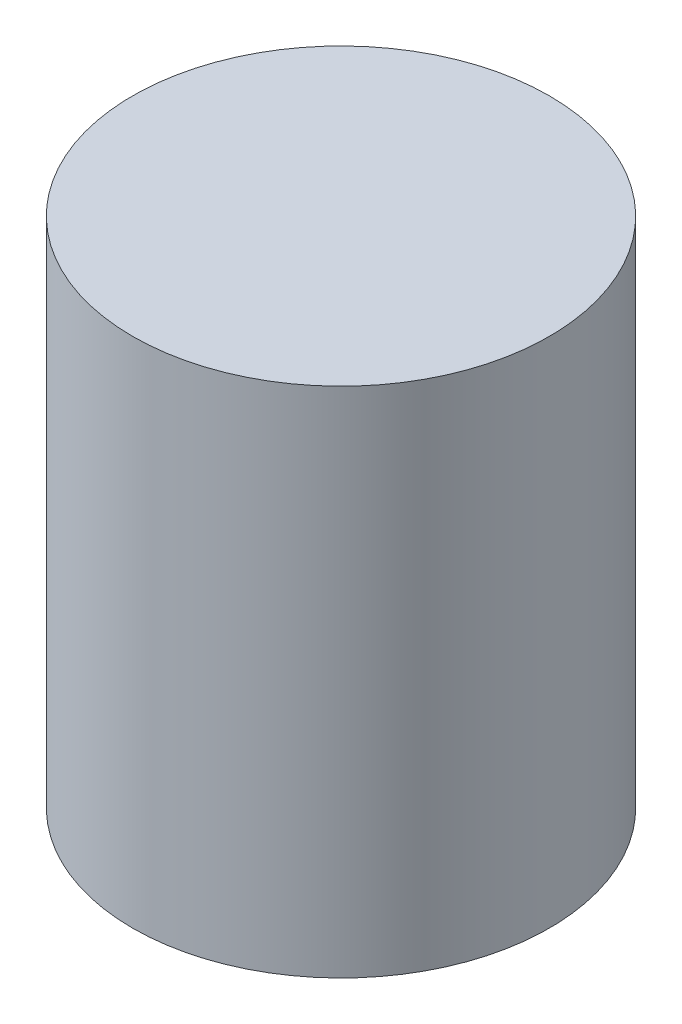
SolidWorks part; units mm, degrees
ref_plane "前视基准面" through (0, 0, 0) normal (0, 0, 1) x (1, 0, 0)
ref_plane "上视基准面" through (0, 0, 0) normal (0, 1, 0) x (1, 0, 0)
ref_plane "右视基准面" through (0, 0, 0) normal (1, 0, 0) x (0, 0, -1)
sketch "草图1" plane through (0, 0, 0) normal (0, 1, 0) x (1, 0, 0)
  circle A0 centre (-8.111, 1.6699) radius 20.3273
extrude "凸台-拉伸3" add sketch "草图1" along normal blind 50 contours A0
